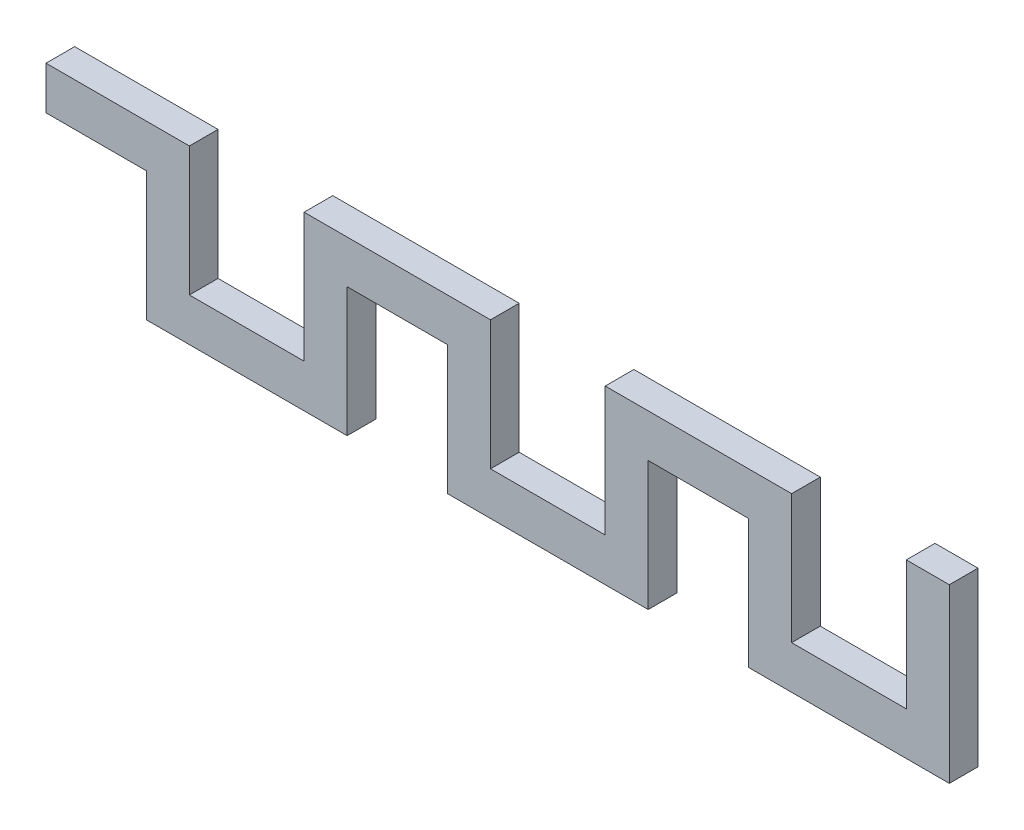
SolidWorks part; units mm, degrees
ref_plane "前视基准面" through (0, 0, 0) normal (0, 0, 1) x (1, 0, 0)
ref_plane "上视基准面" through (0, 0, 0) normal (0, 1, 0) x (1, 0, 0)
ref_plane "右视基准面" through (0, 0, 0) normal (1, 0, 0) x (0, 0, -1)
sketch "草图1" plane through (0, 0, 0) normal (0, 0, 1) x (1, 0, 0)
  line L0 (0, 0) -> (20, 0)
  line L1 (20, 0) -> (20, -18)
  line L2 (20, -18) -> (36, -18)
  line L3 (36, -18) -> (36, 0)
  line L4 (0, 0) -> (0, -6)
  line L5 (0, -6) -> (14, -6)
  line L6 (14, -6) -> (14, -24)
  line L7 (14, -24) -> (42, -24)
  line L8 (42, -24) -> (42, -6)
  line L9 (36, 0) -> (62, 0)
  line L10 (62, 0) -> (62, -18)
  line L11 (62, -18) -> (78, -18)
  line L12 (78, -18) -> (78, 0)
  line L13 (42, -6) -> (56, -6)
  line L14 (56, -6) -> (56, -24)
  line L15 (56, -24) -> (84, -24)
  line L16 (84, -24) -> (84, -6)
  line L17 (78, 0) -> (104, 0)
  line L18 (104, 0) -> (104, -18)
  line L19 (104, -18) -> (120, -18)
  line L20 (120, -18) -> (120, 0)
  line L21 (84, -6) -> (98, -6)
  line L22 (98, -6) -> (98, -24)
  line L23 (98, -24) -> (126, -24)
  line L24 (126, -24) -> (126, -6)
  line L25 (126, -6) -> (126, 0)
  line L26 (126, 0) -> (120, 0)
extrude "凸台-拉伸1" add sketch "草图1" along normal blind 4
